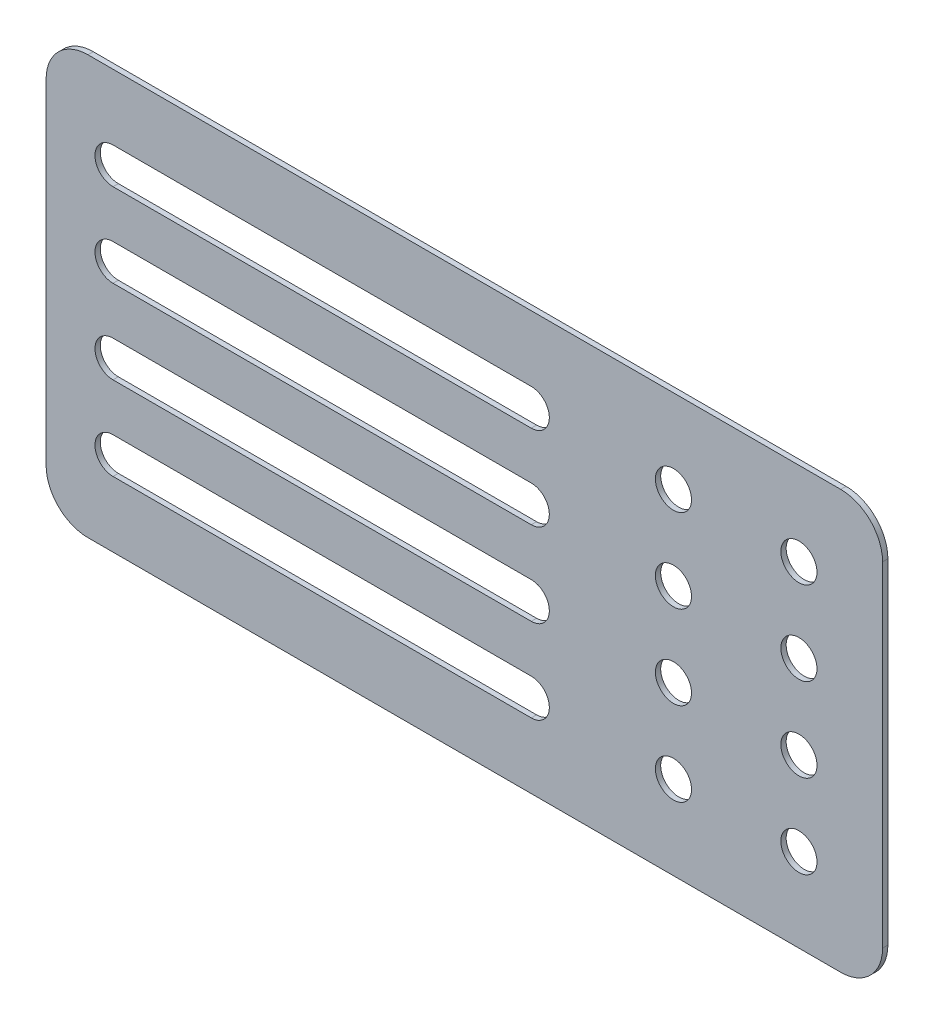
SolidWorks part; units mm, degrees
other "Markup1"
sketch "Sketch2" plane through (0, 0, 0.635) normal (-0.0358, 0.7742, 0.6319) x (0.999, 0.0446, 0.002)
ref_plane "Front Plane" through (0, 0, 0) normal (0, 0, 1) x (1, 0, 0)
ref_plane "Top Plane" through (0, 0, 0) normal (0, 1, 0) x (1, 0, 0)
ref_plane "Right Plane" through (0, 0, 0) normal (1, 0, 0) x (0, 0, -1)
sketch "Sketch1" plane through (0, 0, 0) normal (0, 0, 1) x (1, 0, 0)
  line L0 (8, -10) -> (58, -10) construction
  line L1 (100, 0) -> (0, 0)
  line L2 (100, 0) -> (100, -50)
  line L3 (100, -50) -> (0, -50)
  line L4 (0, 0) -> (0, -50)
  line L9 (8, -7.84) -> (58, -7.84)
  line L12 (8, -12.16) -> (58, -12.16)
  line L13 (8, -22.16) -> (58, -22.16)
  line L14 (8, -17.84) -> (58, -17.84)
  line L15 (8, -20) -> (58, -20) construction
  line L16 (8, -32.16) -> (58, -32.16)
  line L17 (8, -27.84) -> (58, -27.84)
  line L18 (8, -30) -> (58, -30) construction
  line L19 (8, -42.16) -> (58, -42.16)
  line L20 (8, -37.84) -> (58, -37.84)
  line L21 (8, -40) -> (58, -40) construction
  circle A0 centre (75, -10) radius 2.16
  circle A1 centre (90, -10) radius 2.16
  circle A2 centre (35, -10) radius 2.16
  circle A3 centre (35, -20) radius 2.16
  circle A4 centre (75, -20) radius 2.16
  circle A5 centre (90, -20) radius 2.16
  circle A6 centre (35, -30) radius 2.16
  circle A7 centre (75, -30) radius 2.16
  circle A8 centre (90, -30) radius 2.16
  circle A9 centre (35, -40) radius 2.16
  circle A10 centre (75, -40) radius 2.16
  circle A11 centre (90, -40) radius 2.16
  circle A20 centre (75, -10) radius 3.9624 construction
  circle A21 centre (75, -20) radius 3.9624 construction
  arc A22 (8, -7.84) -> (8, -12.16) centre (8, -10) ccw
  arc A23 (58, -12.16) -> (58, -7.84) centre (58, -10) ccw
  arc A24 (8, -17.84) -> (8, -22.16) centre (8, -20) ccw
  arc A25 (58, -22.16) -> (58, -17.84) centre (58, -20) ccw
  arc A26 (8, -27.84) -> (8, -32.16) centre (8, -30) ccw
  arc A27 (58, -32.16) -> (58, -27.84) centre (58, -30) ccw
  arc A28 (8, -37.84) -> (8, -42.16) centre (8, -40) ccw
  arc A29 (58, -42.16) -> (58, -37.84) centre (58, -40) ccw
  point P8 (33, -10)
  point P40 (33, -20)
  point P47 (33, -30)
  point P54 (33, -40)
  dimension "D5" = 4.32
  dimension "D11" = 7.9248
  dimension "D1" = 10
  dimension "D2" = 15
  dimension "D3" = 100
  dimension "D4" = 10
  dimension "D6" = 40
  dimension "D7" = 10
  dimension "D8" = 10
  dimension "D10" = 2
  dimension "D12" = 50
  dimension "D13" = 10
  dimension "D9" = 4
extrude "Boss-Extrude1" add sketch "Sketch1" along normal blind 0.635
fillet "Fillet1" radius 5 4 edges at (100, -50, 0.3175) (0, -50, 0.3175) (100, 0, 0.3175) (0, 0, 0.3175)
